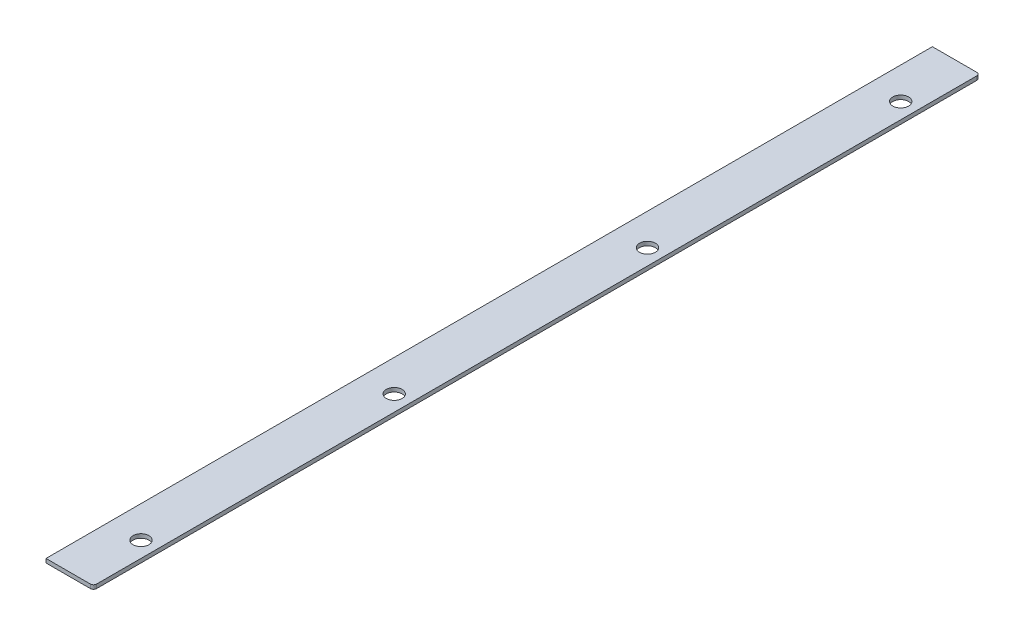
SolidWorks part; units mm, degrees
ref_plane "Front Plane" through (0, 0, 0) normal (0, 0, 1) x (1, 0, 0)
ref_plane "Top Plane" through (0, 0, 0) normal (0, 1, 0) x (1, 0, 0)
ref_plane "Right Plane" through (0, 0, 0) normal (1, 0, 0) x (0, 0, -1)
sketch "Sketch1" plane through (0, 0, 0) normal (0, 1, 0) x (1, 0, 0)
  line L1 (0, 0) -> (38.1, 0)
  line L2 (0, 0) -> (0, 711.2)
  line L3 (0, 711.2) -> (38.1, 711.2)
  line L4 (38.1, 0) -> (38.1, 711.2)
  dimension "D1" = 38.1
  dimension "D2" = 711.2
extrude "Boss-Extrude1" add sketch "Sketch1" along normal blind 3.175
fillet "Fillet1" radius 2.54 2 edges at (38.1, 1.5875, 0) (38.1, 1.5875, -711.2)
sketch "Sketch2" plane through (0, 3.175, 0) normal (0, 1, 0) x (1, 0, 0)
  line L1 (0, 711.2) -> (0, 0) construction
  line L2 (35.56, 711.2) -> (0, 711.2) construction
  circle A0 centre (25.4, 660.4) radius 6.35
  circle A1 centre (25.4, 457.2) radius 6.35
  circle A2 centre (25.4, 254) radius 6.35
  circle A3 centre (25.4, 50.8) radius 6.35
  dimension "D1" = 25.4
  dimension "D3" = 203.2
  dimension "D4" = 203.2
  dimension "D5" = 203.2
  dimension "D2" = 50.8
extrude "Cut-Extrude1" cut sketch "Sketch2" against normal through all
